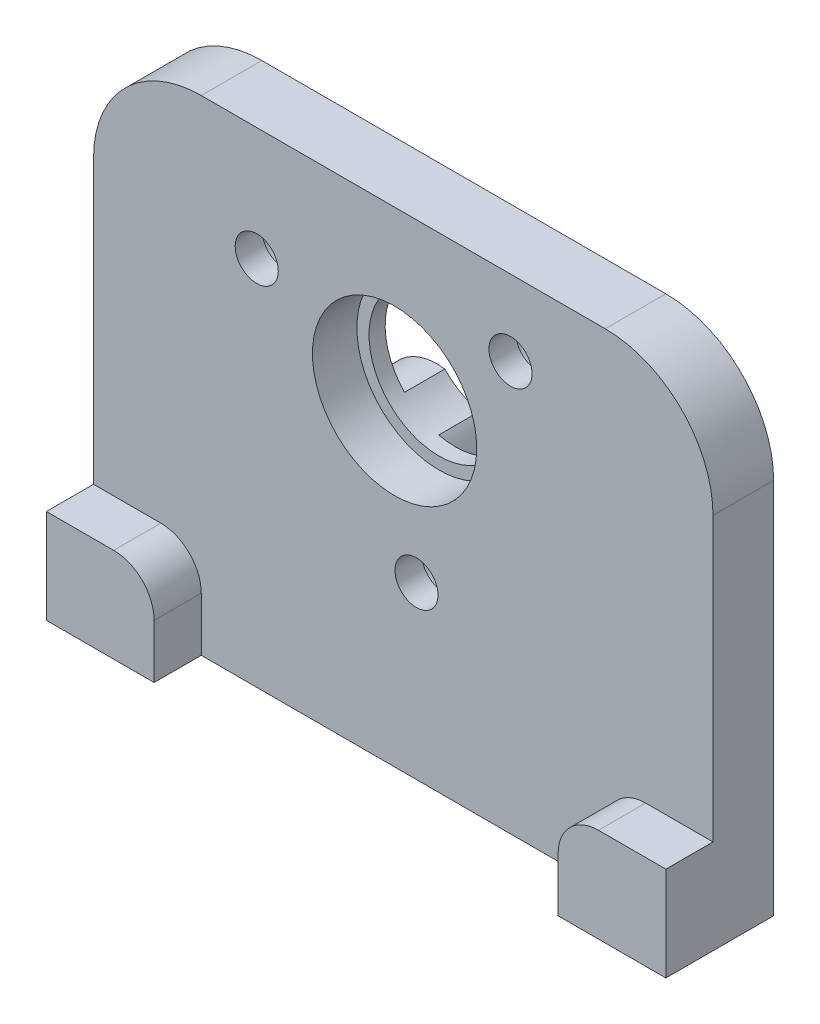
SolidWorks part; units mm, degrees
ref_plane "Front Plane" through (0, 0, 0) normal (0, 0, 1) x (1, 0, 0)
ref_plane "Top Plane" through (0, 0, 0) normal (0, 1, 0) x (1, 0, 0)
ref_plane "Right Plane" through (0, 0, 0) normal (1, 0, 0) x (0, 0, -1)
ref_plane "Plane1" through (0, 0, 4.5) normal (0, 0, 1) x (1, 0, 0)
sketch "Sketch1" plane through (0, 0, 4.5) normal (0, 0, 1) x (1, 0, 0)
  line L0 (23, -18) -> (23, 18)
  line L1 (23, 18) -> (-23, 18)
  line L2 (-23, 18) -> (-23, -18)
  line L3 (-23, -18) -> (23, -18)
extrude "Boss-Extrude1" add sketch "Sketch1" against normal blind 4.5
sketch "Sketch2" plane through (0, 0, 4.5) normal (0, 0, 1) x (1, 0, 0)
  line L0 (-15, -11) -> (-15, -18)
  line L1 (-15, -18) -> (-23, -18)
  line L2 (-23, -18) -> (-23, -11)
  line L3 (-23, -11) -> (-15, -11)
extrude "Boss-Extrude2" add sketch "Sketch2" along normal blind 3.5
sketch "Sketch3" plane through (0, 0, 4.5) normal (0, 0, 1) x (1, 0, 0)
  line L0 (23, -18) -> (15, -18)
  line L1 (15, -18) -> (15, -11)
  line L2 (15, -11) -> (23, -11)
  line L3 (23, -11) -> (23, -18)
extrude "Boss-Extrude3" add sketch "Sketch3" along normal blind 3.5
ref_plane "Plane2" through (0, -2, 0) normal (0, 1, 0) x (1, 0, 0)
sketch "Sketch4" plane through (0, -2, 0) normal (0, 1, 0) x (1, 0, 0)
  line L0 (-1, 3) -> (-5, 3)
  line L1 (-5, 3) -> (-5, 0)
  line L2 (-5, 0) -> (-1, 0)
  line L3 (-1, 0) -> (-1, 3)
  line L4 (-5, 3) -> (-5, 0) construction
revolve "Revolve1" add sketch "Sketch4" angle 360 about L4
hole_wizard "Ø2.05 (2.05) Diameter Hole1" positions "Sketch6" profile "Sketch5" hole size "Ø2.05" standard "ANSI Metric"
sketch "Sketch6" plane through (0, -18, 0) normal (0, -1, 0) x (-1, 0, 0)
  point P0 (0, -2.25)
sketch "Sketch5" plane through (0, -18, 2.25) normal (1, 0, 0) x (0, 0, -1)
  line L0 (0, 0) -> (0, 8.6159)
  line L1 (0, 8.6159) -> (1.025, 8)
  line L2 (1.025, 8) -> (1.025, 0)
  line L5 (1.025, 0) -> (0, 0)
  line L10 (0, 8.6159) -> (-1.025, 8) construction
  line L11 (0, -6.35) -> (0, 107.95) construction
  dimension "Hole Dia." = 2.05
  dimension "Hole Depth" = 8
  dimension "Drill Angle" = 118
hole_wizard "Ø2.5 (2.5) Diameter Hole1" positions "Sketch8" profile "Sketch7" hole size "Ø2.5" standard "ANSI Metric"
sketch "Sketch8" plane through (0, -18, 0) normal (0, -1, 0) x (-1, 0, 0)
  point P0 (19, -4)
  point P1 (-19, -4)
sketch "Sketch7" plane through (-19, -18, 4) normal (1, 0, 0) x (0, 0, -1)
  line L0 (0, 0) -> (0, 6.7511)
  line L1 (0, 6.7511) -> (1.25, 6)
  line L2 (1.25, 6) -> (1.25, 0)
  line L5 (1.25, 0) -> (0, 0)
  line L10 (0, 6.7511) -> (-1.25, 6) construction
  line L11 (0, -6.35) -> (0, 107.95) construction
  dimension "Hole Dia." = 2.5
  dimension "Hole Depth" = 6
  dimension "Drill Angle" = 118
hole_wizard "CBORE for M3 Hex Head Machine Screw1" positions "Sketch10" profile "Sketch9" counterbore size "M3" standard "ANSI Metric"
sketch "Sketch10" plane through (0, 0, 0) normal (0, 0, -1) x (-1, 0, 0)
  point P0 (-7.9629, 12.3894)
  point P1 (10.8804, 9.5732)
  point P2 (-0.9801, -5.3374)
sketch "Sketch9" plane through (7.9629, 12.3894, 0) normal (1, 0, 0) x (0, 1, 0)
  line L0 (0, 0) -> (0, 8)
  line L1 (0, 8) -> (1.6, 8)
  line L3 (1.6, 8) -> (1.6, 2.5)
  line L4 (1.6, 2.5) -> (2.7, 2.5)
  line L5 (2.7, 2.5) -> (2.7, 0)
  line L7 (2.7, 0) -> (0, 0)
  line L11 (0, -6.35) -> (0, 107.95) construction
  dimension "Thru Hole Dia." = 3.2
  dimension "Thru Hole Depth" = 8
  dimension "C'Bore Dia." = 5.4
  dimension "C'Bore Depth" = 2.5
hole_wizard "Hole1" positions "Sketch12" profile "Sketch11" legacy end condition through all
sketch "Sketch12" plane through (0, 0, 4.5) normal (0, 0, 1) x (1, 0, 0)
  point P0 (-0.6458, 5.5417)
sketch "Sketch11" plane through (-0.6458, 5.5417, 4.5) normal (1, 0, 0) x (0, -1, 0)
  line L0 (0, 0) -> (0, 7.5)
  line L1 (0, 7.5) -> (5.2, 7.5)
  line L2 (5.2, 7.5) -> (5.2, 3.3)
  line L3 (5.2, 3.3) -> (6.1, 3.3)
  line L4 (6.1, 3.3) -> (6.1, 0)
  line L5 (6.1, 0) -> (0, 0)
  line L6 (0, 110) -> (0, -10) construction
  dimension "Diameter" = 10.4
  dimension "Depth" = 7.5
  dimension "C-Bore Diameter" = 12.2
  dimension "C-Bore Depth" = 3.3
hole_wizard "Ø4.2 (4.2) Diameter Hole1" positions "Sketch14" profile "Sketch13" hole size "Ø4.2" standard "ANSI Metric"
sketch "Sketch14" plane through (0, 0, -3) normal (0, 0, -1) x (-1, 0, 0)
  point P0 (5, -2)
sketch "Sketch13" plane through (-5, -2, -3) normal (1, 0, 0) x (0, 1, 0)
  line L0 (0, 0) -> (0, 7)
  line L1 (0, 7) -> (2.1, 7)
  line L2 (2.1, 7) -> (2.1, 0)
  line L5 (2.1, 0) -> (0, 0)
  line L10 (0, 7) -> (-2.1, 7) construction
  line L11 (0, -6.35) -> (0, 107.95) construction
  dimension "Hole Dia." = 4.2
  dimension "Hole Depth" = 7
  dimension "Drill Angle" = 180
fillet "Fillet1" radius 3 2 edges at (-15, -11, 6.25) (15, -11, 6.25)
fillet "Fillet2" radius 8 2 edges at (23, 18, 2.25) (-23, 18, 2.25)
